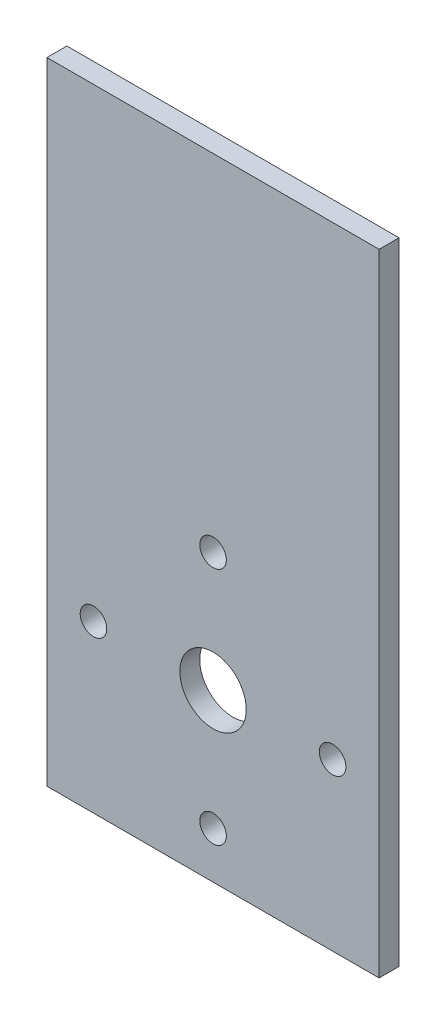
SolidWorks part; units mm, degrees
material "Plain Carbon Steel"
ref_plane "Front Plane" through (0, 0, 0) normal (0, 0, 1) x (1, 0, 0)
ref_plane "Top Plane" through (0, 0, 0) normal (0, 1, 0) x (1, 0, 0)
ref_plane "Right Plane" through (0, 0, 0) normal (1, 0, 0) x (0, 0, -1)
sketch "Sketch1" plane through (0, 0, 0) normal (0, 0, 1) x (1, 0, 0)
  line L0 (-25, 95) -> (25, 95)
  line L1 (-25, 0) -> (25, 0)
  line L2 (-25, 95) -> (-25, 0)
  line L3 (25, 95) -> (25, 0)
  circle A0 centre (0, 25) radius 5
  point P6 (0, 0)
  dimension "D5" = 10
  dimension "D6" = 25
  dimension "D7" = 25
  dimension "D1" = 50
  dimension "D2" = 95
  dimension "D3" = 25
  dimension "D4" = 50
extrude "Boss-Extrude1" add sketch "Sketch1" along normal blind 3
sketch "Sketch2" plane through (0, 0, 3) normal (0, 0, 1) x (1, 0, 0)
  line L0 (-25, 0) -> (25, 0) construction
  line L1 (25, 0) -> (25, 95) construction
  circle A0 centre (0, 43) radius 2
  circle A1 centre (0, 25) radius 5 construction
  circle A2 centre (18, 25) radius 2
  circle A3 centre (0, 7) radius 2
  circle A4 centre (-18, 25) radius 2
  dimension "D1" = 4
  dimension "D3" = 2
  dimension "D4" = 18
  dimension "D5" = 4
  dimension "D6" = 18
  dimension "D7" = 4
  dimension "D8" = 18
  dimension "D9" = 25
  dimension "D10" = 25
  dimension "D11" = 25
  dimension "D12" = 36
  dimension "D2" = 18
extrude "Cut-Extrude3" cut sketch "Sketch2" against normal blind 10
